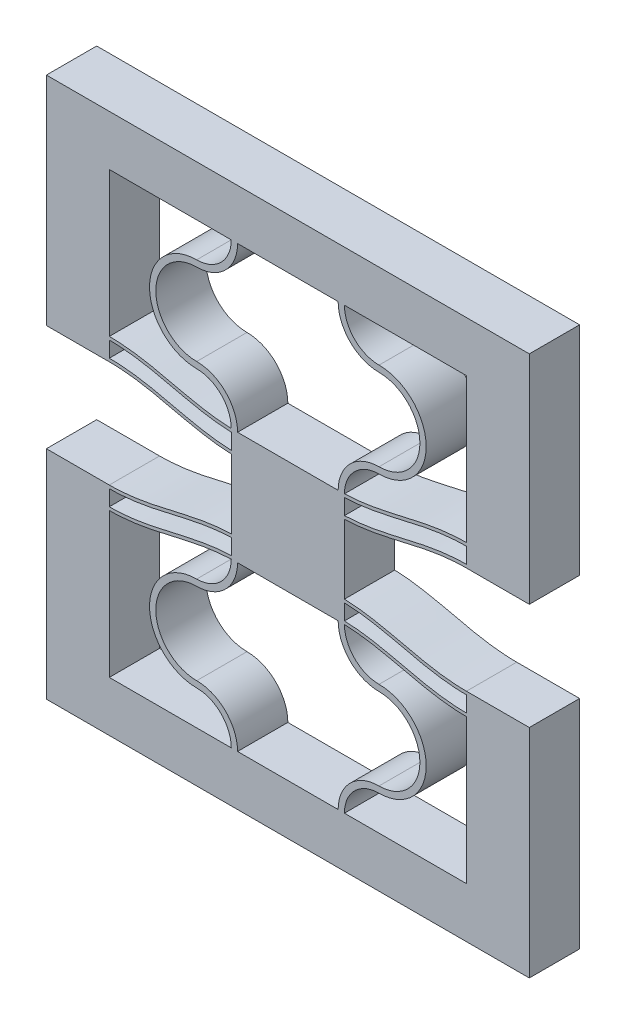
SolidWorks part; units mm, degrees
ref_plane "Front Plane" through (0, 0, 0) normal (0, 0, 1) x (1, 0, 0)
ref_plane "Top Plane" through (0, 0, 0) normal (0, 1, 0) x (1, 0, 0)
ref_plane "Right Plane" through (0, 0, 0) normal (1, 0, 0) x (0, 0, -1)
sketch "Sketch1" plane through (0, 0, 0) normal (0, 0, 1) x (1, 0, 0)
  line L4 (0, 11.5) -> (0, 0)
  line L5 (10.2, 0) -> (10.2, 13) construction
  line L6 (10.2, 13) -> (10.2, 15.9911) construction
  line L17 (9.7, 0) -> (0, 0)
  line L18 (10.7, 0) -> (20.4, 0)
  line L19 (20.4, 0) -> (20.4, 11.5)
  line L20 (10.7, 13.2411) -> (10.7, 14.4911)
  line L21 (9.7, 13.2411) -> (9.7, 14.4911)
  line L22 (10.7, 14.7411) -> (10.7, 15.9911)
  line L23 (10.7, 15.9911) -> (9.7, 15.9911)
  line L24 (9.7, 15.9911) -> (9.7, 14.7411)
  line L31 (-5, 13.25) -> (-5, -4)
  line L32 (-5, -4) -> (25.4, -4)
  line L33 (25.4, -4) -> (25.4, 13.25)
  line L34 (0, 11.75) -> (0, 13)
  line L36 (-5, 13.25) -> (0, 13.25)
  line L37 (25.4, 13.25) -> (20.4, 13.25)
  line L38 (20.4, 11.75) -> (20.4, 13)
  arc A0 (10.2, 13) -> (6.95, 9.75) centre (6.95, 13) cw
  arc A1 (6.95, 9.75) -> (6.95, 3.25) centre (6.95, 6.5) ccw
  arc A2 (6.95, 3.25) -> (10.2, 0) centre (6.95, 0) cw
  arc A3 (9.7, 12.9911) -> (6.95, 10.25) centre (6.95, 13) cw
  arc A4 (6.95, 10.25) -> (6.95, 2.75) centre (6.95, 6.5) ccw
  arc A5 (6.95, 2.75) -> (9.7, 0) centre (6.95, 0) cw
  arc A6 (9.7, 13) -> (6.95, 10.25) centre (6.95, 13) cw construction
  arc A7 (13.45, 3.25) -> (10.2, 0) centre (13.45, 0) ccw
  arc A8 (13.45, 2.75) -> (10.7, 0) centre (13.45, 0) ccw
  arc A9 (13.45, 9.75) -> (13.45, 3.25) centre (13.45, 6.5) cw
  arc A10 (13.45, 10.25) -> (13.45, 2.75) centre (13.45, 6.5) cw
  arc A11 (10.7, 12.9911) -> (13.45, 10.25) centre (13.45, 13) ccw
  arc A12 (10.2, 13) -> (13.45, 9.75) centre (13.45, 13) ccw
  spline S0 degree 4 poles (-2.0401, 11.8932) (-1.9772, 11.8846) (-1.8455, 11.8679) (-1.6624, 11.8447) (-1.3945, 11.8179) (-1.0936, 11.7897) (-0.7437, 11.7688) (-0.4752, 11.7554) (-0.0408, 11.749) (0.1102, 11.7499) (0.4738, 11.7558) (0.7092, 11.7679) (1.0334, 11.7851) (1.3516, 11.8128) (1.7502, 11.854) (2.1923, 11.9124) (2.7058, 11.9922) (3.3058, 12.1029) (4.0022, 12.2485) (4.9166, 12.4561) (5.9838, 12.707) (7.055, 12.9379) (8.1373, 13.1142) (9.0337, 13.2105) (9.8109, 13.2536) (10.5891, 13.2536) (11.3663, 13.2105) (12.2627, 13.1142) (13.3449, 12.9379) (14.4163, 12.707) (15.4832, 12.4561) (16.3198, 12.2662) (16.8578, 12.1523) (17.3629, 12.0533) (17.7764, 11.9798) (18.2035, 11.9124) (18.6563, 11.854) (18.9878, 11.8179) (19.2899, 11.793) (19.5137, 11.7765) (19.7423, 11.7659) (19.9174, 11.7558) (20.2941, 11.7499) (20.4363, 11.749) (20.8074, 11.7542) (21.0192, 11.7634) (21.2671, 11.7754) (21.4449, 11.7884) (21.6432, 11.8037) (21.8311, 11.8212) (22.0262, 11.8414) (22.2161, 11.864) (22.3445, 11.8804) (22.4082, 11.8889) (22.4399, 11.8932) knots 0 0 0 0 0 0.010394 0.020788 0.031182 0.041576 0.062112 0.07238 0.082649 0.098356 0.106209 0.114063 0.12977 0.145477 0.161184 0.176891 0.202819 0.228747 0.260161 0.291575 0.354403 0.405758 0.437172 0.468586 0.5 0.531414 0.562828 0.594242 0.645597 0.708425 0.739839 0.771253 0.784217 0.797181 0.823109 0.838816 0.854523 0.87023 0.878084 0.885937 0.893791 0.901644 0.917351 0.92762 0.937888 0.948156 0.958424 0.963621 0.968818 0.979212 0.989606 0.994803 1 1 1 1 1 construction
  spline S1 degree 4 poles (0, 11.75) (0.0812, 11.75) (0.1997, 11.7513) (0.4738, 11.7558) (0.7092, 11.7679) (1.0334, 11.7851) (1.3516, 11.8128) (1.7502, 11.854) (2.1923, 11.9124) (2.7058, 11.9922) (3.3058, 12.1029) (4.0022, 12.2485) (4.9166, 12.4561) (5.9838, 12.707) (7.055, 12.9379) (8.1373, 13.1142) (9.0337, 13.2105) (9.8109, 13.2536) (10.5891, 13.2536) (11.3663, 13.2105) (12.2627, 13.1142) (13.3449, 12.9379) (14.4163, 12.707) (15.4832, 12.4561) (16.3198, 12.2662) (16.8578, 12.1523) (17.3629, 12.0533) (17.7764, 11.9798) (18.2035, 11.9124) (18.6563, 11.854) (18.9878, 11.8179) (19.2899, 11.793) (19.5137, 11.7765) (19.7423, 11.7659) (19.9174, 11.7558) (20.2013, 11.7513) (20.3188, 11.75) (20.4, 11.75) knots 0.082649 0.082649 0.082649 0.082649 0.082649 0.098356 0.106209 0.114063 0.12977 0.145477 0.161184 0.176891 0.202819 0.228747 0.260161 0.291575 0.354403 0.405758 0.437172 0.468586 0.5 0.531414 0.562828 0.594242 0.645597 0.708425 0.739839 0.771253 0.784217 0.797181 0.823109 0.838816 0.854523 0.87023 0.878084 0.885937 0.893791 0.901644 0.917351 0.917351 0.917351 0.917351 0.917351
  spline S2 degree 4 poles (-2.0401, 13.1432) (-1.9772, 13.1346) (-1.8455, 13.1179) (-1.6624, 13.0947) (-1.3945, 13.0679) (-1.0936, 13.0397) (-0.7437, 13.0188) (-0.4752, 13.0054) (-0.0408, 12.999) (0.1102, 12.9999) (0.4738, 13.0058) (0.7092, 13.0179) (1.0334, 13.0351) (1.3516, 13.0628) (1.7502, 13.104) (2.1923, 13.1624) (2.7058, 13.2422) (3.3058, 13.3529) (4.0022, 13.4985) (4.9166, 13.7061) (5.9838, 13.957) (7.055, 14.1879) (8.1373, 14.3642) (9.0337, 14.4605) (9.8109, 14.5036) (10.5891, 14.5036) (11.3663, 14.4605) (12.2627, 14.3642) (13.3449, 14.1879) (14.4163, 13.957) (15.4832, 13.7061) (16.3198, 13.5162) (16.8578, 13.4023) (17.3629, 13.3033) (17.7764, 13.2298) (18.2035, 13.1624) (18.6563, 13.104) (18.9878, 13.0679) (19.2899, 13.043) (19.5137, 13.0265) (19.7423, 13.0159) (19.9174, 13.0058) (20.2941, 12.9999) (20.4363, 12.999) (20.8074, 13.0042) (21.0192, 13.0134) (21.2671, 13.0254) (21.4449, 13.0384) (21.6432, 13.0537) (21.8311, 13.0712) (22.0262, 13.0914) (22.2161, 13.114) (22.3445, 13.1304) (22.4082, 13.1389) (22.4399, 13.1432) knots 0 0 0 0 0 0.010394 0.020788 0.031182 0.041576 0.062112 0.07238 0.082649 0.098356 0.106209 0.114063 0.12977 0.145477 0.161184 0.176891 0.202819 0.228747 0.260161 0.291575 0.354403 0.405758 0.437172 0.468586 0.5 0.531414 0.562828 0.594242 0.645597 0.708425 0.739839 0.771253 0.784217 0.797181 0.823109 0.838816 0.854523 0.87023 0.878084 0.885937 0.893791 0.901644 0.917351 0.92762 0.937888 0.948156 0.958424 0.963621 0.968818 0.979212 0.989606 0.994803 1 1 1 1 1 construction
  spline S3 degree 4 poles (0, 13) (0.0812, 13) (0.1997, 13.0013) (0.4738, 13.0058) (0.7092, 13.0179) (1.0334, 13.0351) (1.3516, 13.0628) (1.7502, 13.104) (2.1923, 13.1624) (2.7058, 13.2422) (3.3058, 13.3529) (4.0022, 13.4985) (4.9166, 13.7061) (5.9838, 13.957) (7.055, 14.1879) (8.1373, 14.3642) (9.0337, 14.4605) (9.8109, 14.5036) (10.5891, 14.5036) (11.3663, 14.4605) (12.2627, 14.3642) (13.3449, 14.1879) (14.4163, 13.957) (15.4832, 13.7061) (16.3198, 13.5162) (16.8578, 13.4023) (17.3629, 13.3033) (17.7764, 13.2298) (18.2035, 13.1624) (18.6563, 13.104) (18.9878, 13.0679) (19.2899, 13.043) (19.5137, 13.0265) (19.7423, 13.0159) (19.9174, 13.0058) (20.2013, 13.0013) (20.3188, 13) (20.4, 13) knots 0.082649 0.082649 0.082649 0.082649 0.082649 0.098356 0.106209 0.114063 0.12977 0.145477 0.161184 0.176891 0.202819 0.228747 0.260161 0.291575 0.354403 0.405758 0.437172 0.468586 0.5 0.531414 0.562828 0.594242 0.645597 0.708425 0.739839 0.771253 0.784217 0.797181 0.823109 0.838816 0.854523 0.87023 0.878084 0.885937 0.893791 0.901644 0.917351 0.917351 0.917351 0.917351 0.917351
  spline S4 degree 4 poles (-2.0401, 13.3932) (-1.9772, 13.3846) (-1.8455, 13.3679) (-1.6624, 13.3447) (-1.3945, 13.3179) (-1.0936, 13.2897) (-0.7437, 13.2688) (-0.4752, 13.2554) (-0.0408, 13.249) (0.1102, 13.2499) (0.4738, 13.2558) (0.7092, 13.2679) (1.0334, 13.2851) (1.3516, 13.3128) (1.7502, 13.354) (2.1923, 13.4124) (2.7058, 13.4922) (3.3058, 13.6029) (4.0022, 13.7485) (4.9166, 13.9561) (5.9838, 14.207) (7.055, 14.4379) (8.1373, 14.6142) (9.0337, 14.7105) (9.8109, 14.7536) (10.5891, 14.7536) (11.3663, 14.7105) (12.2627, 14.6142) (13.3449, 14.4379) (14.4163, 14.207) (15.4832, 13.9561) (16.3198, 13.7662) (16.8578, 13.6523) (17.3629, 13.5533) (17.7764, 13.4798) (18.2035, 13.4124) (18.6563, 13.354) (18.9878, 13.3179) (19.2899, 13.293) (19.5137, 13.2765) (19.7423, 13.2659) (19.9174, 13.2558) (20.2941, 13.2499) (20.4363, 13.249) (20.8074, 13.2542) (21.0192, 13.2634) (21.2671, 13.2754) (21.4449, 13.2884) (21.6432, 13.3037) (21.8311, 13.3212) (22.0262, 13.3414) (22.2161, 13.364) (22.3445, 13.3804) (22.4082, 13.3889) (22.4399, 13.3932) knots 0 0 0 0 0 0.010394 0.020788 0.031182 0.041576 0.062112 0.07238 0.082649 0.098356 0.106209 0.114063 0.12977 0.145477 0.161184 0.176891 0.202819 0.228747 0.260161 0.291575 0.354403 0.405758 0.437172 0.468586 0.5 0.531414 0.562828 0.594242 0.645597 0.708425 0.739839 0.771253 0.784217 0.797181 0.823109 0.838816 0.854523 0.87023 0.878084 0.885937 0.893791 0.901644 0.917351 0.92762 0.937888 0.948156 0.958424 0.963621 0.968818 0.979212 0.989606 0.994803 1 1 1 1 1 construction
  spline S5 degree 4 poles (0, 13.25) (0.0812, 13.25) (0.1997, 13.2513) (0.4738, 13.2558) (0.7092, 13.2679) (1.0334, 13.2851) (1.3516, 13.3128) (1.7502, 13.354) (2.1923, 13.4124) (2.7058, 13.4922) (3.3058, 13.6029) (4.0022, 13.7485) (4.9166, 13.9561) (5.9838, 14.207) (7.055, 14.4379) (8.1373, 14.6142) (9.0337, 14.7105) (9.8109, 14.7536) (10.5891, 14.7536) (11.3663, 14.7105) (12.2627, 14.6142) (13.3449, 14.4379) (14.4163, 14.207) (15.4832, 13.9561) (16.3198, 13.7662) (16.8578, 13.6523) (17.3629, 13.5533) (17.7764, 13.4798) (18.2035, 13.4124) (18.6563, 13.354) (18.9878, 13.3179) (19.2899, 13.293) (19.5137, 13.2765) (19.7423, 13.2659) (19.9174, 13.2558) (20.2013, 13.2513) (20.3188, 13.25) (20.4, 13.25) knots 0.082649 0.082649 0.082649 0.082649 0.082649 0.098356 0.106209 0.114063 0.12977 0.145477 0.161184 0.176891 0.202819 0.228747 0.260161 0.291575 0.354403 0.405758 0.437172 0.468586 0.5 0.531414 0.562828 0.594242 0.645597 0.708425 0.739839 0.771253 0.784217 0.797181 0.823109 0.838816 0.854523 0.87023 0.878084 0.885937 0.893791 0.901644 0.917351 0.917351 0.917351 0.917351 0.917351
  spline S8 degree 4 poles (-2.0401, 11.6432) (-1.9772, 11.6346) (-1.8455, 11.6179) (-1.6624, 11.5947) (-1.3945, 11.5679) (-1.0936, 11.5397) (-0.7437, 11.5188) (-0.4752, 11.5054) (-0.0408, 11.499) (0.1102, 11.4999) (0.4738, 11.5058) (0.7092, 11.5179) (1.0334, 11.5351) (1.3516, 11.5628) (1.7502, 11.604) (2.1923, 11.6624) (2.7058, 11.7422) (3.3058, 11.8529) (4.0022, 11.9985) (4.9166, 12.2061) (5.9838, 12.457) (7.055, 12.6879) (8.1373, 12.8642) (9.0337, 12.9605) (9.8109, 13.0036) (10.5891, 13.0036) (11.3663, 12.9605) (12.2627, 12.8642) (13.3449, 12.6879) (14.4163, 12.457) (15.4832, 12.2061) (16.3198, 12.0162) (16.8578, 11.9023) (17.3629, 11.8033) (17.7764, 11.7298) (18.2035, 11.6624) (18.6563, 11.604) (18.9878, 11.5679) (19.2899, 11.543) (19.5137, 11.5265) (19.7423, 11.5159) (19.9174, 11.5058) (20.2941, 11.4999) (20.4363, 11.499) (20.8074, 11.5042) (21.0192, 11.5134) (21.2671, 11.5254) (21.4449, 11.5384) (21.6432, 11.5537) (21.8311, 11.5712) (22.0262, 11.5914) (22.2161, 11.614) (22.3445, 11.6304) (22.4082, 11.6389) (22.4399, 11.6432) knots 0 0 0 0 0 0.010394 0.020788 0.031182 0.041576 0.062112 0.07238 0.082649 0.098356 0.106209 0.114063 0.12977 0.145477 0.161184 0.176891 0.202819 0.228747 0.260161 0.291575 0.354403 0.405758 0.437172 0.468586 0.5 0.531414 0.562828 0.594242 0.645597 0.708425 0.739839 0.771253 0.784217 0.797181 0.823109 0.838816 0.854523 0.87023 0.878084 0.885937 0.893791 0.901644 0.917351 0.92762 0.937888 0.948156 0.958424 0.963621 0.968818 0.979212 0.989606 0.994803 1 1 1 1 1 construction
  spline S9 degree 4 poles (0, 11.5) (0.0812, 11.5) (0.1997, 11.5013) (0.4738, 11.5058) (0.7092, 11.5179) (1.0334, 11.5351) (1.3516, 11.5628) (1.7502, 11.604) (2.1923, 11.6624) (2.7058, 11.7422) (3.3058, 11.8529) (4.0022, 11.9985) (4.9166, 12.2061) (5.9838, 12.457) (7.055, 12.6879) (8.1373, 12.8642) (9.0337, 12.9605) (9.8109, 13.0036) (10.5891, 13.0036) (11.3663, 12.9605) (12.2627, 12.8642) (13.3449, 12.6879) (14.4163, 12.457) (15.4832, 12.2061) (16.3198, 12.0162) (16.8578, 11.9023) (17.3629, 11.8033) (17.7764, 11.7298) (18.2035, 11.6624) (18.6563, 11.604) (18.9878, 11.5679) (19.2899, 11.543) (19.5137, 11.5265) (19.7423, 11.5159) (19.9174, 11.5058) (20.2013, 11.5013) (20.3188, 11.5) (20.4, 11.5) knots 0.082649 0.082649 0.082649 0.082649 0.082649 0.098356 0.106209 0.114063 0.12977 0.145477 0.161184 0.176891 0.202819 0.228747 0.260161 0.291575 0.354403 0.405758 0.437172 0.468586 0.5 0.531414 0.562828 0.594242 0.645597 0.708425 0.739839 0.771253 0.784217 0.797181 0.823109 0.838816 0.854523 0.87023 0.878084 0.885937 0.893791 0.901644 0.917351 0.917351 0.917351 0.917351 0.917351
  point P5 (9.7, 13.2411)
  point P10 (9.7, 14.4911)
  point P22 (10.7, 13.2411)
  point P28 (10.7, 14.4911)
  point P29 (10.7, 14.7411)
  point P32 (9.7, 14.7411)
  point P34 (21.4279, 13)
  point P35 (20.4727, 13.25)
  dimension "D4" = 0.25
  dimension "D6" = 4
  dimension "D1" = 13
  dimension "D2" = 0.5
  dimension "D3" = 0.25
  dimension "D7" = 5
  dimension "D5" = 1.5
extrude "Boss-Extrude1" add sketch "Sketch1" along normal blind 4
sketch "Sketch4" plane through (0, 15.9911, 0) normal (0, 1, 0) x (1, 0, 0)
  line L24 (10.7, 0) -> (9.7, 0)
  line L25 (9.7, 0) -> (9.7, -4)
  line L26 (10.7, 0) -> (9.7, 0)
  line L27 (10.7, -4) -> (10.7, 0)
  line L29 (9.7, 0) -> (9.7, -4)
  line L31 (10.7, -4) -> (10.7, 0)
  line L32 (9.7, -4) -> (10.7, -4)
  line L33 (9.7, -4) -> (10.7, -4)
  dimension "D1" = 0
extrude "Boss-Extrude2" add sketch "Sketch4" along normal blind 1.5
mirror "Mirror3" about plane through (0, 17.4911, 0) normal (0, 1, 0) of bodies 179
ref_plane "Plane1" through (10.2, 0, 0) normal (-1, 0, 0) x (0, 0, 1)
split "Split2" trim tools "Plane1" bodies to split 247 102 resulting bodies 225
sketch "Sketch7" plane through (10.2, 0, 0) normal (-1, 0, 0) x (0, 0, 1)
  line L4 (4, 34.9822) -> (4, 38.9822)
  line L12 (0, 13) -> (4, 13)
  line L13 (0, 13) -> (4, 13)
  line L14 (4, 13) -> (4, 21.9822)
  line L15 (4, 13) -> (4, 21.9822)
  line L20 (4, 0) -> (0, 0)
  line L22 (4, 0) -> (0, 0)
  line L23 (0, -4) -> (4, -4)
  line L27 (0, -4) -> (4, -4)
  line L31 (4, 21.9822) -> (0, 21.9822)
  line L32 (4, 21.9822) -> (0, 21.9822)
  line L33 (0, 21.9822) -> (0, 13)
  line L34 (0, 21.9822) -> (0, 13)
  line L36 (4, -4) -> (4, 0)
  line L38 (4, 34.9822) -> (4, 38.9822)
  line L39 (4, 34.9822) -> (4, 38.9822)
  line L40 (4, 38.9822) -> (0, 38.9822)
  line L41 (4, 38.9822) -> (0, 38.9822)
  line L46 (4, 34.9822) -> (4, 38.9822)
  line L51 (0, 38.9822) -> (0, 34.9822)
  line L52 (0, 38.9822) -> (0, 34.9822)
  line L53 (0, 34.9822) -> (4, 34.9822)
  line L54 (0, 34.9822) -> (4, 34.9822)
  line L55 (4, 38.9822) -> (0, 38.9822)
  line L57 (4, 38.9822) -> (0, 38.9822)
  line L59 (4, -4) -> (4, 0)
  line L60 (0, 0) -> (0, -4)
  line L61 (0, 0) -> (0, -4)
  line L62 (0, 38.9822) -> (0, 34.9822)
  line L63 (0, 38.9822) -> (0, 34.9822)
  line L64 (0, 34.9822) -> (4, 34.9822)
  line L65 (0, 34.9822) -> (4, 34.9822)
  dimension "D1" = 0
  dimension "D2" = 0
  dimension "D3" = 0
  dimension "D4" = 0
extrude "Boss-Extrude3" add sketch "Sketch7" along normal blind 4
mirror "Mirror2" about plane through (6.2, 0, 0) normal (-1, 0, 0) of bodies 226
